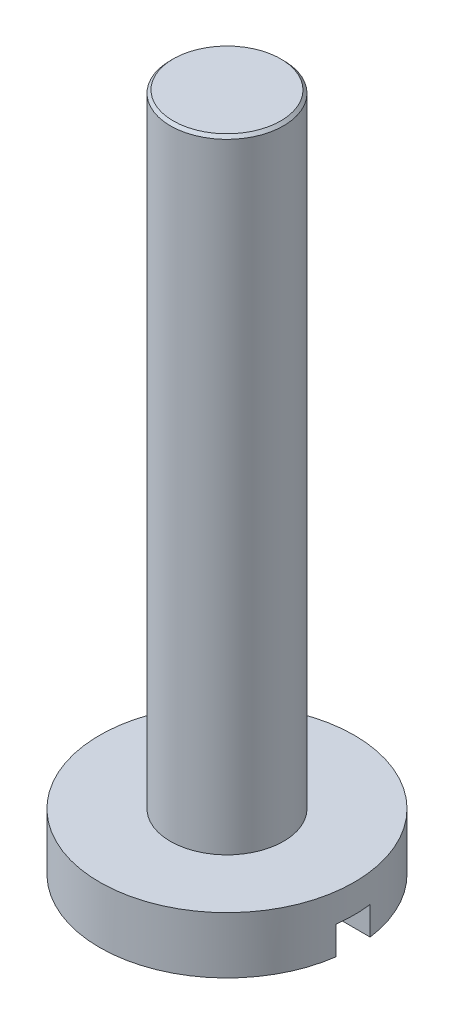
SolidWorks part; units mm, degrees
ref_plane "Front Plane" through (0, 0, 0) normal (0, 0, 1) x (1, 0, 0)
ref_plane "Top Plane" through (0, 0, 0) normal (0, 1, 0) x (1, 0, 0)
ref_plane "Right Plane" through (0, 0, 0) normal (1, 0, 0) x (0, 0, -1)
sketch "Sketch1" plane through (0, 0, 0) normal (0, 1, 0) x (1, 0, 0)
  circle A0 centre (0, 0) radius 1
  dimension "D1" = 2
extrude "Boss-Extrude1" add sketch "Sketch1" along normal blind 11
cosmetic thread "Cosmetic Thread1" parameters "D2"=1.548
sketch "Sketch2" plane through (0, 0, 0) normal (0, -1, 0) x (1, 0, 0)
  circle A0 centre (0, 0) radius 2.25
  circle A1 centre (0, 0) radius 1
  circle A2 centre (0, 0) radius 1 construction
  dimension "D1" = 0
  dimension "D2" = 1.25
extrude "Boss-Extrude2" add sketch "Sketch2" along normal blind 1 separate body
sketch "Sketch3" plane through (0, -1, 0) normal (0, -1, 0) x (1, 0, 0)
  line L1 (-4.0982, -0.3) -> (4.0982, -0.3)
  line L2 (-4.0982, -0.3) -> (-4.0982, 0.3)
  line L3 (-4.0982, 0.3) -> (4.0982, 0.3)
  line L4 (4.0982, -0.3) -> (4.0982, 0.3)
  line L5 (-4.0982, -0.3) -> (4.0982, 0.3) construction
  line L6 (-4.0982, 0.3) -> (4.0982, -0.3) construction
  point P0 (0, 0)
  dimension "D1" = 0.6
extrude "Cut-Extrude1" cut sketch "Sketch3" against normal blind 0.5
chamfer "Chamfer1" distance 0.05 angle 45 1 edges at (0, 11, 1)
